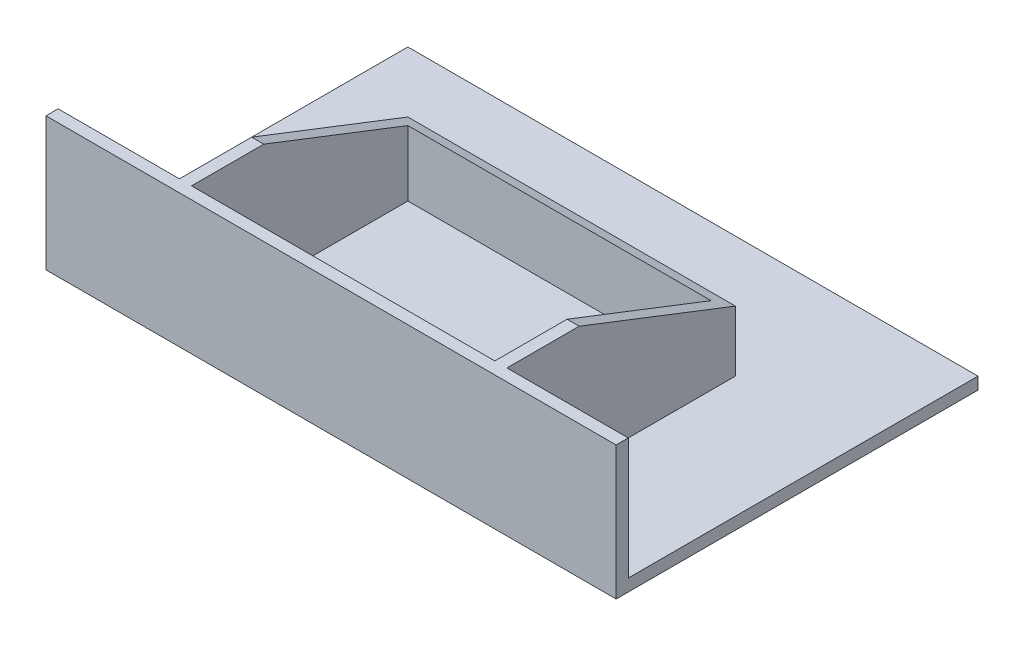
SolidWorks part; units mm, degrees
ref_plane "Alzado" through (0, 0, 0) normal (0, 0, 1) x (1, 0, 0)
ref_plane "Planta" through (0, 0, 0) normal (0, 1, 0) x (1, 0, 0)
ref_plane "Vista lateral" through (0, 0, 0) normal (1, 0, 0) x (0, 0, -1)
sketch "Croquis1" plane through (0, 0, 0) normal (1, 0, 0) x (0, 0, -1)
  line L0 (0, 0) -> (42521.936, 0) construction
  line L1 (0, 0) -> (0, 42521.936) construction
  line L2 (0, 0) -> (0, 20)
  line L3 (0, 20) -> (11.9075, 20)
  line L4 (11.9075, 20) -> (37.6612, 10)
  line L5 (37.6612, 10) -> (37.6612, 0)
  line L6 (37.6612, 0) -> (0, 0)
  circle A0 centre (4, 5) radius 2.1
  dimension "D1" = 4.2
  dimension "D2" = 20
  dimension "D3" = 10
  dimension "D4" = 4
  dimension "D5" = 5
extrude "Saliente-Extruir1" add sketch "Croquis1" along normal mid plane 54
sketch "Croquis2" plane through (0, 20, 0) normal (0, 1, 0) x (1, 0, 0)
  line L0 (-27, 37.6612) -> (-27, 11.9075) construction
  line L1 (-25, 0) -> (25, 0)
  line L2 (-25, 0) -> (-25, 35.6612)
  line L3 (-25, 35.6612) -> (25, 35.6612)
  line L4 (25, 0) -> (25, 35.6612)
  line L5 (-25, 0) -> (25, 35.6612) construction
  line L6 (-25, 35.6612) -> (25, 0) construction
  line L7 (27, 37.6612) -> (27, 11.9075) construction
  line L9 (27, 37.6612) -> (-27, 37.6612) construction
  line L10 (27, 0) -> (-27, 0) construction
  point P4 (0, 17.8306)
  point P9 (25, 0)
  dimension "D1" = 2
  dimension "D2" = 2
  dimension "D4" = 2
extrude "Cortar-Extruir1" cut sketch "Croquis2" against normal up to surface (20 mm away) up to face at (0, 0, -18.8306)
sketch "Croquis3" plane through (0, 0, 0) normal (0, 0, 1) x (1, 0, 0)
  line L0 (0, 0) -> (0, 50000) construction
  line L1 (-25, 0) -> (25, 0) construction
  line L2 (-47, 20) -> (47, 20)
  line L3 (-47, 20) -> (-47, -2)
  line L4 (-47, -2) -> (47, -2)
  line L5 (47, 20) -> (47, -2)
  line L6 (-47, 20) -> (47, -2) construction
  line L7 (-47, -2) -> (47, 20) construction
  line L8 (27, 20) -> (27, 0) construction
  line L9 (27, 20) -> (25, 20) construction
  point P3 (0, 9)
  dimension "D1" = 2
  dimension "D2" = 20
extrude "Saliente-Extruir2" add sketch "Croquis3" along normal blind 2
sketch "Croquis4" plane through (0, 0, 0) normal (0, -1, 0) x (1, 0, 0)
  line L0 (27, -37.6612) -> (-27, -37.6612) construction
  line L1 (-47, 0) -> (47, 0)
  line L2 (-47, 0) -> (-47, -57.6612)
  line L3 (-47, -57.6612) -> (47, -57.6612)
  line L4 (47, 0) -> (47, -57.6612)
  line L5 (-47, 0) -> (47, -57.6612) construction
  line L6 (-47, -57.6612) -> (47, 0) construction
  point P4 (0, -28.8306)
  point P6 (47, 0)
  dimension "D1" = 20
extrude "Saliente-Extruir3" add sketch "Croquis4" along normal up to surface (2 mm away) up to face at (0, -2, 1)
